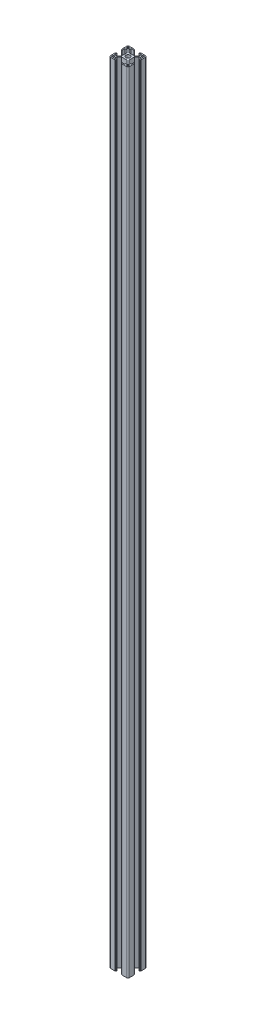
SolidWorks part; units mm, degrees
material "6063-T5"
ref_plane "前视基准面" through (0, 0, 0) normal (0, 0, 1) x (1, 0, 0)
ref_plane "上视基准面" through (0, 0, 0) normal (0, 1, 0) x (1, 0, 0)
ref_plane "右视基准面" through (0, 0, 0) normal (1, 0, 0) x (0, 0, -1)
sketch "草图3" plane through (0, 0, 0) normal (0, 1, 0) x (1, 0, 0)
  line L0 (0, 0) -> (-15, -15) construction
  line L1 (-15, -15) -> (-15, 0) construction
  line L2 (-15, 0) -> (0, 0) construction
  line L3 (-15, -12.5) -> (-15, -5.4)
  line L4 (-14.8, -5.2) -> (-14.4, -5.2)
  line L5 (-14.2, -5) -> (-14.2, -4.3)
  line L6 (-14, -4.1) -> (-13.2, -4.1)
  line L7 (-13.2, -4.1) -> (-13.2, -8.25)
  line L8 (-13.2, -8.25) -> (-9.5228, -8.25)
  line L9 (-9.5228, -8.25) -> (-5.8, -4.5272)
  line L10 (-5.8, -4.5272) -> (-5.8, 4.5272)
  line L11 (-13.2, -12.2) -> (-13.2, -11.05)
  line L12 (-12.2, -10.05) -> (-11.05, -10.05)
  line L13 (-4.5272, -5.8) -> (4.5272, -5.8)
  line L14 (-8.25, -9.5228) -> (-4.5272, -5.8)
  line L15 (-12.2, -13.2) -> (-11.05, -13.2)
  line L16 (-10.05, -12.2) -> (-10.05, -11.05)
  line L17 (-5.2, -14.8) -> (-5.2, -14.4)
  line L18 (-5, -14.2) -> (-4.3, -14.2)
  line L19 (-4.1, -14) -> (-4.1, -13.2)
  line L20 (-4.1, -13.2) -> (-8.25, -13.2)
  line L21 (-8.25, -13.2) -> (-8.25, -9.5228)
  line L22 (-12.5, -15) -> (-5.4, -15)
  line L23 (-12.5, 15) -> (-5.4, 15)
  line L24 (-8.25, 13.2) -> (-8.25, 9.5228)
  line L25 (-4.1, 13.2) -> (-8.25, 13.2)
  line L26 (-4.1, 14) -> (-4.1, 13.2)
  line L27 (-5, 14.2) -> (-4.3, 14.2)
  line L28 (-5.2, 14.8) -> (-5.2, 14.4)
  line L29 (-10.05, 12.2) -> (-10.05, 11.05)
  line L30 (-12.2, 13.2) -> (-11.05, 13.2)
  line L31 (-8.25, 9.5228) -> (-4.5272, 5.8)
  line L32 (-4.5272, 5.8) -> (4.5272, 5.8)
  line L33 (-12.2, 10.05) -> (-11.05, 10.05)
  line L34 (-13.2, 12.2) -> (-13.2, 11.05)
  line L35 (-9.5228, 8.25) -> (-5.8, 4.5272)
  line L36 (-13.2, 8.25) -> (-9.5228, 8.25)
  line L37 (-13.2, 4.1) -> (-13.2, 8.25)
  line L38 (-14, 4.1) -> (-13.2, 4.1)
  line L39 (-14.2, 5) -> (-14.2, 4.3)
  line L40 (-14.8, 5.2) -> (-14.4, 5.2)
  line L41 (-15, 12.5) -> (-15, 5.4)
  line L42 (0, 0) -> (0, -12.3268) construction
  line L43 (15, 12.5) -> (15, 5.4)
  line L44 (14.8, 5.2) -> (14.4, 5.2)
  line L45 (14.2, 5) -> (14.2, 4.3)
  line L46 (14, 4.1) -> (13.2, 4.1)
  line L47 (13.2, 4.1) -> (13.2, 8.25)
  line L48 (13.2, 8.25) -> (9.5228, 8.25)
  line L49 (9.5228, 8.25) -> (5.8, 4.5272)
  line L50 (13.2, 12.2) -> (13.2, 11.05)
  line L51 (12.2, 10.05) -> (11.05, 10.05)
  line L52 (8.25, 9.5228) -> (4.5272, 5.8)
  line L53 (12.2, 13.2) -> (11.05, 13.2)
  line L54 (10.05, 12.2) -> (10.05, 11.05)
  line L55 (5.2, 14.8) -> (5.2, 14.4)
  line L56 (5, 14.2) -> (4.3, 14.2)
  line L57 (4.1, 14) -> (4.1, 13.2)
  line L58 (4.1, 13.2) -> (8.25, 13.2)
  line L59 (8.25, 13.2) -> (8.25, 9.5228)
  line L60 (12.5, 15) -> (5.4, 15)
  line L61 (12.5, -15) -> (5.4, -15)
  line L62 (8.25, -13.2) -> (8.25, -9.5228)
  line L63 (4.1, -13.2) -> (8.25, -13.2)
  line L64 (4.1, -14) -> (4.1, -13.2)
  line L65 (5, -14.2) -> (4.3, -14.2)
  line L66 (5.2, -14.8) -> (5.2, -14.4)
  line L67 (10.05, -12.2) -> (10.05, -11.05)
  line L68 (12.2, -13.2) -> (11.05, -13.2)
  line L69 (8.25, -9.5228) -> (4.5272, -5.8)
  line L70 (12.2, -10.05) -> (11.05, -10.05)
  line L71 (13.2, -12.2) -> (13.2, -11.05)
  line L72 (5.8, -4.5272) -> (5.8, 4.5272)
  line L73 (9.5228, -8.25) -> (5.8, -4.5272)
  line L74 (13.2, -8.25) -> (9.5228, -8.25)
  line L75 (13.2, -4.1) -> (13.2, -8.25)
  line L76 (14, -4.1) -> (13.2, -4.1)
  line L77 (14.2, -5) -> (14.2, -4.3)
  line L78 (14.8, -5.2) -> (14.4, -5.2)
  line L79 (15, -12.5) -> (15, -5.4)
  circle A0 centre (0, 0) radius 3.4
  arc A1 (-12.5, 15) -> (-15, 12.5) centre (-12.5, 12.5) ccw
  arc A2 (15, 12.5) -> (12.5, 15) centre (12.5, 12.5) ccw
  arc A3 (12.5, -15) -> (15, -12.5) centre (12.5, -12.5) ccw
  arc A4 (-15, -12.5) -> (-12.5, -15) centre (-12.5, -12.5) ccw
  arc A5 (-12.2, 13.2) -> (-13.2, 12.2) centre (-12.2, 12.2) ccw
  arc A6 (-12.2, 10.05) -> (-13.2, 11.05) centre (-12.2, 11.05) cw
  arc A7 (-10.05, 11.05) -> (-11.05, 10.05) centre (-11.05, 11.05) cw
  arc A8 (-10.05, 12.2) -> (-11.05, 13.2) centre (-11.05, 12.2) ccw
  arc A9 (11.05, 10.05) -> (10.05, 11.05) centre (11.05, 11.05) cw
  arc A10 (11.05, 13.2) -> (10.05, 12.2) centre (11.05, 12.2) ccw
  arc A11 (13.2, 12.2) -> (12.2, 13.2) centre (12.2, 12.2) ccw
  arc A12 (13.2, 11.05) -> (12.2, 10.05) centre (12.2, 11.05) cw
  arc A13 (12.2, -10.05) -> (13.2, -11.05) centre (12.2, -11.05) cw
  arc A14 (10.05, -11.05) -> (11.05, -10.05) centre (11.05, -11.05) cw
  arc A15 (10.05, -12.2) -> (11.05, -13.2) centre (11.05, -12.2) ccw
  arc A16 (12.2, -13.2) -> (13.2, -12.2) centre (12.2, -12.2) ccw
  arc A17 (-13.2, -11.05) -> (-12.2, -10.05) centre (-12.2, -11.05) cw
  arc A18 (-11.05, -10.05) -> (-10.05, -11.05) centre (-11.05, -11.05) cw
  arc A19 (-11.05, -13.2) -> (-10.05, -12.2) centre (-11.05, -12.2) ccw
  arc A20 (-13.2, -12.2) -> (-12.2, -13.2) centre (-12.2, -12.2) ccw
  arc A21 (-15, -5.4) -> (-14.8, -5.2) centre (-14.8, -5.4) cw
  arc A22 (-14.4, -5.2) -> (-14.2, -5) centre (-14.4, -5) ccw
  arc A23 (-14.2, -4.3) -> (-14, -4.1) centre (-14, -4.3) cw
  arc A24 (-14, 4.1) -> (-14.2, 4.3) centre (-14, 4.3) cw
  arc A25 (-14.2, 5) -> (-14.4, 5.2) centre (-14.4, 5) ccw
  arc A26 (-14.8, 5.2) -> (-15, 5.4) centre (-14.8, 5.4) cw
  arc A27 (-5.4, 15) -> (-5.2, 14.8) centre (-5.4, 14.8) cw
  arc A28 (-5, 14.2) -> (-5.2, 14.4) centre (-5, 14.4) cw
  arc A29 (-4.1, 14) -> (-4.3, 14.2) centre (-4.3, 14) ccw
  arc A30 (5.2, 14.8) -> (5.4, 15) centre (5.4, 14.8) cw
  arc A31 (5.2, 14.4) -> (5, 14.2) centre (5, 14.4) cw
  arc A32 (4.3, 14.2) -> (4.1, 14) centre (4.3, 14) ccw
  arc A33 (15, 5.4) -> (14.8, 5.2) centre (14.8, 5.4) cw
  arc A34 (14.4, 5.2) -> (14.2, 5) centre (14.4, 5) ccw
  arc A35 (14.2, 4.3) -> (14, 4.1) centre (14, 4.3) cw
  arc A36 (14, -4.1) -> (14.2, -4.3) centre (14, -4.3) cw
  arc A37 (14.2, -5) -> (14.4, -5.2) centre (14.4, -5) ccw
  arc A38 (14.8, -5.2) -> (15, -5.4) centre (14.8, -5.4) cw
  arc A39 (5.4, -15) -> (5.2, -14.8) centre (5.4, -14.8) cw
  arc A40 (5, -14.2) -> (5.2, -14.4) centre (5, -14.4) cw
  arc A41 (4.1, -14) -> (4.3, -14.2) centre (4.3, -14) ccw
  arc A42 (-5.2, -14.4) -> (-5, -14.2) centre (-5, -14.4) cw
  arc A43 (-4.3, -14.2) -> (-4.1, -14) centre (-4.3, -14) ccw
  arc A44 (-5.2, -14.8) -> (-5.4, -15) centre (-5.4, -14.8) cw
  point P38 (-5.8, 0)
  point P46 (0, 5.8)
  point P47 (0, -5.8)
  point P83 (5.8, 0)
  point P87 (-15, 15)
  point P90 (15, 15)
  point P93 (15, -15)
  point P99 (-13.2, 13.2)
  point P102 (-13.2, 10.05)
  point P105 (-10.05, 10.05)
  point P108 (-10.05, 13.2)
  point P111 (10.05, 10.05)
  point P114 (10.05, 13.2)
  point P117 (13.2, 13.2)
  point P120 (13.2, 10.05)
  point P123 (13.2, -10.05)
  point P126 (10.05, -10.05)
  point P129 (10.05, -13.2)
  point P132 (13.2, -13.2)
  point P135 (-13.2, -10.05)
  point P138 (-10.05, -10.05)
  point P141 (-10.05, -13.2)
  point P144 (-13.2, -13.2)
  point P147 (-15, -5.2)
  point P150 (-14.2, -5.2)
  point P153 (-14.2, -4.1)
  point P156 (-14.2, 4.1)
  point P159 (-14.2, 5.2)
  point P162 (-15, 5.2)
  point P165 (-5.2, 15)
  point P168 (-5.2, 14.2)
  point P171 (-4.1, 14.2)
  point P174 (5.2, 15)
  point P177 (5.2, 14.2)
  point P180 (4.1, 14.2)
  point P183 (15, 5.2)
  point P186 (14.2, 5.2)
  point P189 (14.2, 4.1)
  point P192 (14.2, -4.1)
  point P195 (14.2, -5.2)
  point P198 (15, -5.2)
  point P201 (5.2, -15)
  point P204 (5.2, -14.2)
  point P207 (4.1, -14.2)
  point P210 (-5.2, -14.2)
  point P213 (-4.1, -14.2)
  point P216 (-5.2, -15)
  dimension "D11" = 6.8
  dimension "D12" = 2.5
  dimension "D13" = 1
  dimension "D14" = 0.2
  dimension "D2" = 15
  dimension "D3" = 4.1
  dimension "D4" = 5.2
  dimension "D5" = 0.8
  dimension "D6" = 1.8
  dimension "D7" = 9.2
  dimension "D8" = 8.25
  dimension "D9" = 0.9
  dimension "D10" = 1.8
extrude "凸台-拉伸1" add sketch "草图3" along normal blind 1248.8
